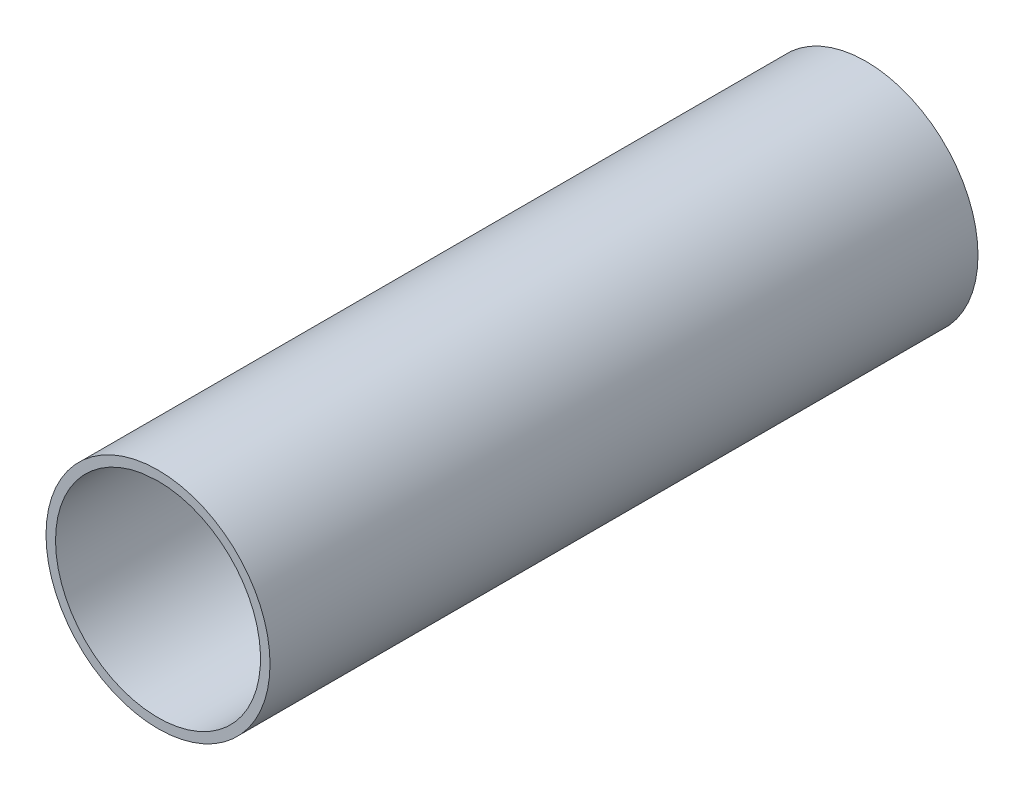
SolidWorks part; units mm, degrees
ref_plane "Спереди" through (0, 0, 0) normal (0, 0, 1) x (1, 0, 0)
ref_plane "Сверху" through (0, 0, 0) normal (0, 1, 0) x (1, 0, 0)
ref_plane "Справа" through (0, 0, 0) normal (1, 0, 0) x (0, 0, -1)
sketch "Эскиз2" plane through (0, 0, 0) normal (0, 0, 1) x (1, 0, 0)
  circle A0 centre (0, 0) radius 20
  circle A1 centre (0, 0) radius 18.3
  dimension "D1" = 40
  dimension "D2" = 36.6
extrude "Бобышка-Вытянуть1" add sketch "Эскиз2" along normal blind 126.4
sketch "Эскиз5" plane through (0, 0, 0) normal (0, 0, -1) x (-1, 0, 0)
  line L0 (0, 0) -> (0, 18.3) construction
  line L1 (0, 0) -> (2.9899, 18.0541) construction
  line L2 (0, 18.3) -> (0, 9.2195)
  line L3 (2.9899, 18.0541) -> (1.5063, 9.0957)
  circle A0 centre (0, 0) radius 18.3 construction
  arc A1 (0, 18.3) -> (2.9899, 18.0541) centre (0, 0) cw
  arc A2 (1.5063, 9.0957) -> (3.3753, 3.6888) centre (7.4257, 8.1154) ccw
  circle A3 centre (0, 0) radius 3
  arc A4 (-2.7273, 4.1907) -> (3.3753, 3.6888) centre (0, 0) ccw
  arc A5 (0, 9.2195) -> (-2.7273, 4.1907) centre (-6, 9.2195) cw
  point P16 (0, 5)
  dimension "D2" = 5
  dimension "D3" = 6
  dimension "D4" = 6
  dimension "D1" = 3
extrude "Бобышка-Вытянуть3" add sketch "Эскиз5" against normal through all
sketch "Sketch1" plane through (0, 0, 0) normal (0, 0, -1) x (-1, 0, 0)
  line L0 (0, 18.3) -> (2.9899, 18.0541)
  arc A0 (0, 18.3) -> (2.9899, 18.0541) centre (0, 0) ccw construction
  arc A2 (0, 18.3) -> (2.9899, 18.0541) centre (0, 0) ccw
extrude "Cut-Extrude1" cut sketch "Sketch1" against normal blind 59
sketch "Sketch2" plane through (0, 0, 126.4) normal (0, 0, 1) x (1, 0, 0)
  line L0 (0, 18.3) -> (-2.9899, 18.0541)
  arc A2 (0, 18.3) -> (-2.9899, 18.0541) centre (0, 0) cw
  arc A3 (-2.9899, 18.0541) -> (0, 18.3) centre (0, 0) ccw construction
extrude "Cut-Extrude2" cut sketch "Sketch2" against normal blind 59
sketch "Sketch3" plane through (0, 0, 0) normal (0, 0, 1) x (1, 0, 0)
  line L0 (5, 0) -> (5, 16.5617)
  line L1 (-5, 0) -> (-5, 16.5617)
  circle A0 centre (0, 0) radius 5 construction
  circle A1 centre (0, 0) radius 3
  arc A2 (5, 0) -> (-5, 0) centre (0, 0) cw
  arc A3 (5, 16.5617) -> (-5, 16.5617) centre (0, 0) ccw
  arc A4 (-2.9899, 18.0541) -> (0, 18.3) centre (0, 0) ccw construction
  dimension "D1" = 10
  dimension "D2" = 6
  dimension "D3" = 1
extrude "Boss-Extrude6" add sketch "Sketch3" along normal offset from surface (58.6 mm away) 0.4 separate body up to face at (-0.7271, 8.8405, 59)
